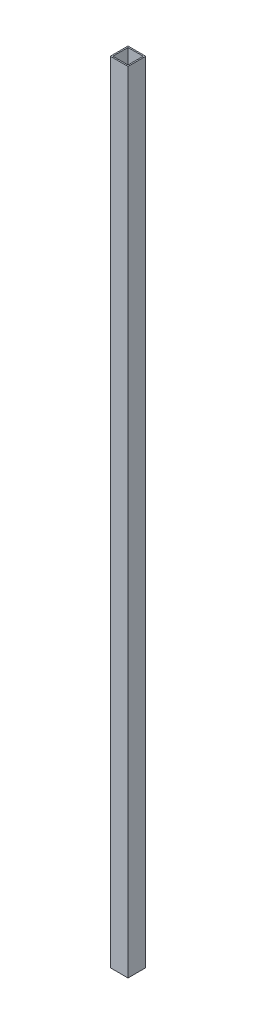
SolidWorks part; units mm, degrees
material "6063-T6"
ref_plane "Front Plane" through (0, 0, 0) normal (0, 0, 1) x (1, 0, 0)
ref_plane "Top Plane" through (0, 0, 0) normal (0, 1, 0) x (1, 0, 0)
ref_plane "Right Plane" through (0, 0, 0) normal (1, 0, 0) x (0, 0, -1)
sketch "Sketch1" plane through (0, 0, 0) normal (0, 1, 0) x (1, 0, 0)
  line L0 (41.275, 3.175) -> (41.275, 41.275)
  line L1 (0, 0) -> (44.45, 0)
  line L2 (0, 0) -> (0, 44.45)
  line L3 (0, 44.45) -> (44.45, 44.45)
  line L4 (44.45, 0) -> (44.45, 44.45)
  line L5 (3.175, 41.275) -> (41.275, 41.275)
  line L6 (3.175, 3.175) -> (3.175, 41.275)
  line L7 (3.175, 3.175) -> (41.275, 3.175)
  dimension "D1" = 44.45
  dimension "D2" = 3.175
extrude "Boss-Extrude1" add sketch "Sketch1" along normal blind 1981.2
sketch "Sketch2" plane through (0, 0, 0) normal (0, 0, 1) x (1, 0, 0)
  line L0 (0, 0) -> (44.45, 0) construction
  line L1 (44.45, 1981.2) -> (44.45, 0) construction
  circle A0 centre (22.225, 22.225) radius 18.2562
  circle A1 centre (22.225, 911.225) radius 18.2563
  dimension "D1" = 889
  dimension "D4" = 36.5125
  dimension "D2" = 22.225
  dimension "D3" = 22.225
extrude "Cut-Extrude1" [suppressed] cut sketch "Sketch2" against normal up to next
sketch "Sketch3" plane through (44.45, 0, 0) normal (1, 0, 0) x (0, 0, -1)
  line L0 (44.45, 1981.2) -> (44.45, 0) construction
  line L1 (0, 0) -> (44.45, 0) construction
  circle A0 centre (22.225, 22.225) radius 4.7625
  circle A1 centre (22.225, 911.225) radius 4.7625
  dimension "D1" = 889
  dimension "D4" = 9.525
  dimension "D2" = 22.225
  dimension "D3" = 22.225
sketch "Sketch4" [suppressed] plane through (0, 0, -44.45) normal (0, 0, -1) x (-1, 0, 0)
  circle A0 centre (-22.225, 911.225) radius 12.7
  circle A1 centre (-22.225, 22.225) radius 12.7
  dimension "D1" = 25.4
extrude "Cut-Extrude2" [suppressed] cut sketch "Sketch4" against normal up to next
